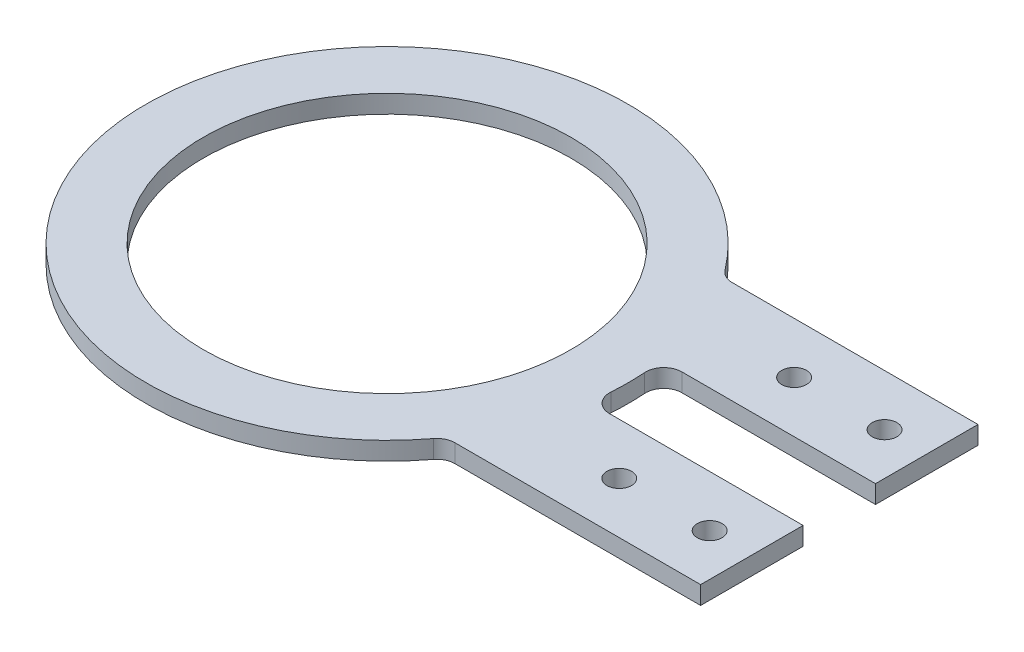
SolidWorks part; units mm, degrees
ref_plane "Front Plane" through (0, 0, 0) normal (0, 0, 1) x (1, 0, 0)
ref_plane "Top Plane" through (0, 0, 0) normal (0, 1, 0) x (1, 0, 0)
ref_plane "Right Plane" through (0, 0, 0) normal (1, 0, 0) x (0, 0, -1)
sketch "Sketch1" plane through (0, 0, 0) normal (0, 1, 0) x (1, 0, 0)
  circle A0 centre (0, 0) radius 40
  circle A1 centre (0, 0) radius 30.5
  dimension "D1" = 80
  dimension "D2" = 61
extrude "Boss-Extrude1" add sketch "Sketch1" along normal blind 3
sketch "Sketch2" plane through (0, 3, 0) normal (0, 1, 0) x (1, 0, 0)
  line L1 (32.7261, 23) -> (75, 23)
  line L2 (32.7261, 23) -> (32.7261, 6)
  line L3 (32.7261, 6) -> (75, 6)
  line L4 (75, 23) -> (75, 6)
  line L5 (32.7261, -6) -> (75, -6)
  line L6 (32.7261, -6) -> (32.7261, -23)
  line L7 (32.7261, -23) -> (75, -23)
  line L8 (75, -6) -> (75, -23)
  circle A1 centre (0, 0) radius 40 construction
  point P4 (0, 0)
  point P11 (35, 23.9633)
  dimension "D1" = 17
  dimension "D2" = 12
  dimension "D3" = 75
  dimension "D5" = 6
extrude "Boss-Extrude2" add sketch "Sketch2" against normal up to surface (3 mm away) up to face at (0, 0, 40)
sketch "Sketch3" plane through (0, 3, 0) normal (0, 1, 0) x (1, 0, 0)
  line L0 (75, 6) -> (75, 23) construction
  line L1 (75, -23) -> (75, -6) construction
  line L2 (53, 14.5) -> (68, 14.5) construction
  line L3 (53, 14.5) -> (53, -14.5) construction
  line L4 (53, -14.5) -> (68, -14.5) construction
  line L5 (68, 14.5) -> (68, -14.5) construction
  circle A0 centre (53, 14.5) radius 2.05
  circle A1 centre (68, 14.5) radius 2.05
  circle A2 centre (53, -14.5) radius 2.05
  circle A3 centre (68, -14.5) radius 2.05
  point P10 (75, 14.5)
  point P14 (75, -14.5)
  dimension "D1" = 4.1
  dimension "D2" = 15
  dimension "D3" = 7
extrude "Cut-Extrude1" cut sketch "Sketch3" against normal through all
fillet "Fillet1" radius 3 4 edges at (39.5474, 1.5, -6) (32.7261, 1.5, -23) (39.5474, 1.5, 6) (32.7261, 1.5, 23)
